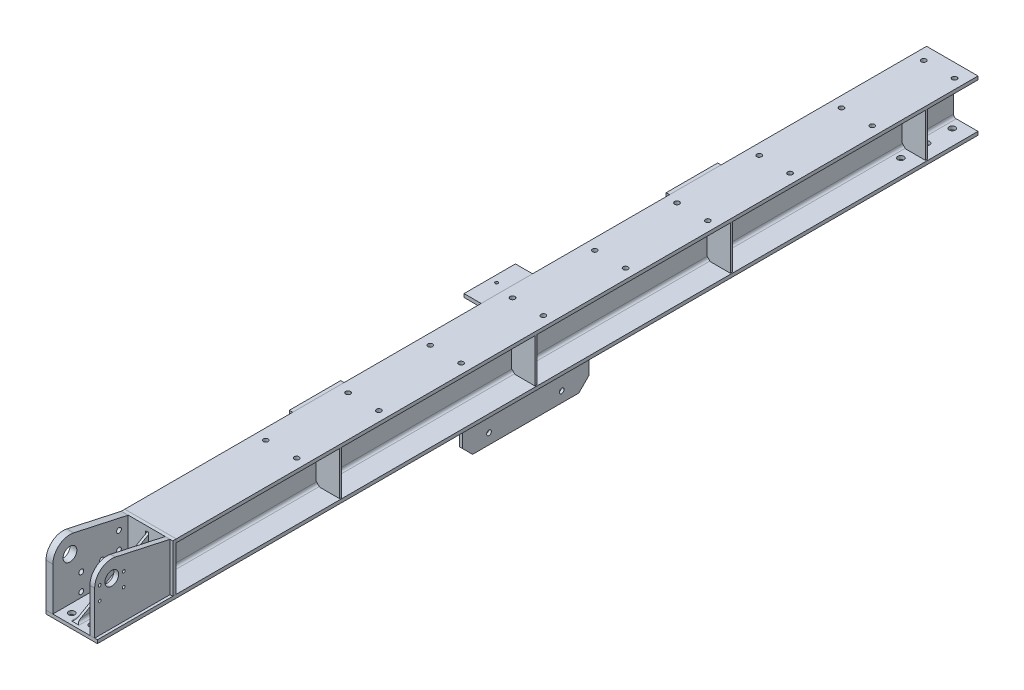
SolidWorks part; units mm, degrees
material "普通碳钢"
ref_plane "前视基准面" through (0, 0, 0) normal (0, 0, 1) x (1, 0, 0)
ref_plane "上视基准面" through (0, 0, 0) normal (0, 1, 0) x (1, 0, 0)
ref_plane "右视基准面" through (0, 0, 0) normal (1, 0, 0) x (0, 0, -1)
sketch "草图1" plane through (0, 0, 0) normal (1, 0, 0) x (0, 0, -1)
  line L0 (-4785.4173, -945.0599) -> (-7355.4173, -945.0599)
  dimension "D1" = 2570
other "H型钢 HW150(1)"
ref_plane "基准面5" through (75, -1020.0599, 4785.4173) normal (0, 0, 1) x (1, 0, 0)
sketch "草图12" plane through (75, -1020.0599, 4785.4173) normal (0, 0, 1) x (1, 0, 0)
  line L0 (-75, -75) -> (75, -75)
  line L1 (75, -75) -> (75, -65)
  line L2 (75, -65) -> (11.5, -65)
  line L3 (3.5, -57) -> (3.5, 57)
  line L4 (11.5, 65) -> (75, 65)
  line L5 (75, 65) -> (75, 75)
  line L6 (75, 75) -> (-75, 75)
  line L7 (0, 75) -> (0, -75) construction
  line L11 (0, 60) -> (0, 75) construction
  line L14 (-75, -75) -> (-75, -65)
  line L15 (-75, -65) -> (-11.5, -65)
  line L16 (-3.5, -57) -> (-3.5, 57)
  line L17 (-11.5, 65) -> (-75, 65)
  line L18 (-75, 65) -> (-75, 75)
  arc A2 (11.5, -65) -> (3.5, -57) centre (11.5, -57) cw
  arc A3 (3.5, 57) -> (11.5, 65) centre (11.5, 57) cw
  arc A5 (-11.5, -65) -> (-3.5, -57) centre (-11.5, -57) ccw
  arc A6 (-3.5, 57) -> (-11.5, 65) centre (-11.5, 57) ccw
  point P2 (0, 0)
  point P38 (0, 0)
  point P39 (75, 75)
  point P40 (75, -75)
  point P41 (-75, -75)
  dimension "D8" = 8
  dimension "D1" = 7
  dimension "D2" = 10
  dimension "D3" = 150
  dimension "D4" = 150
  dimension "D9" = 0
sketch "草图13" plane through (150, 0, 0) normal (1, 0, 0) x (0, 0, -1)
  line L0 (-7355.4173, -945.0599) -> (-7125.4173, -945.0599)
  line L1 (-4785.4173, -945.0599) -> (-7355.4173, -945.0599) construction
  line L2 (-7125.4173, -945.0599) -> (-7125.4173, -960.0599)
  line L6 (-7355.4173, -945.0599) -> (-7355.4173, -1085.0599)
  line L8 (-7355.4173, -1077.0599) -> (-7355.4173, -963.0599) construction
  line L9 (-7355.4173, -1085.0599) -> (-4785.4173, -1085.0599) construction
  line L10 (-7355.4173, -1085.0599) -> (-7345.4173, -1085.0599)
  line L11 (-7355.4173, -1085.0599) -> (-4785.4173, -1085.0599) construction
  line L12 (-7345.4173, -1085.0599) -> (-7125.4173, -960.0599)
  dimension "D1" = 230
  dimension "D2" = 15
  dimension "D3" = 10
extrude "切除-拉伸1" cut sketch "草图13" against normal up to vertex (150 mm away) up to point (0, -945.0599, 7355.4173)
sketch "草图14" plane through (0, 0, 7125.4173) normal (0, 0, 1) x (1, 0, 0)
  line L1 (0, -945.0599) -> (150, -945.0599)
  line L2 (0, -945.0599) -> (0, -1085.0599)
  line L3 (0, -1085.0599) -> (62.0858, -1085.0599)
  line L4 (150, -945.0599) -> (150, -1085.0599)
  line L8 (71, -959.0599) -> (79, -959.0599)
  line L9 (71, -959.0599) -> (71, -1076.1457)
  line L10 (79, -959.0599) -> (79, -1076.1457)
  line L14 (87.9142, -1085.0599) -> (150, -1085.0599)
  line L15 (71.5, -1077.0599) -> (63.5, -1085.0599) construction
  line L16 (71, -1076.1457) -> (62.0858, -1085.0599)
  line L17 (79, -1076.1457) -> (87.9142, -1085.0599)
  line L18 (78.5, -1077.0599) -> (86.5, -1085.0599) construction
  line L19 (79.2721, -1076.4178) -> (87.2071, -1084.3528) construction
  line L20 (70.7284, -1076.4173) -> (62.7929, -1084.3528) construction
  line L23 (78.565, -1077.1249) -> (86.5, -1085.0599) construction
  line L24 (71.4355, -1077.1244) -> (63.5, -1085.0599) construction
  line L25 (78.5, -963.0599) -> (78.5, -1077.0599) construction
  line L26 (71.5, -1077.0599) -> (71.5, -963.0599) construction
  line L27 (70.9162, -960.0599) -> (79.0838, -960.0599) construction
  arc A0 (78.5, -1077.0599) -> (86.5, -1085.0599) centre (86.5, -1077.0599) ccw construction
  point P14 (75, -959.0599)
  dimension "D1" = 0.5
  dimension "D2" = 0.5
  dimension "D3" = 1
  dimension "D4" = 1
  dimension "D5" = 1
extrude "凸台-拉伸1" add sketch "草图14" along normal blind 10 separate body contours L4 L14 L17 L10 L8 L9 L16 L3 L2 L1
sketch "草图15" plane through (0, -1095.0599, 0) normal (0, -1, 0) x (1, 0, 0)
  line L0 (75, 7355.4173) -> (75, 4785.4173) construction
  line L1 (0, 7355.4173) -> (150, 7355.4173) construction
  line L2 (0, 4785.4173) -> (150, 4785.4173) construction
  line L3 (105, 7355.4173) -> (105, 4785.4173) construction
  line L4 (45, 7355.4173) -> (45, 4785.4173) construction
  line L6 (0, 7250.4173) -> (150, 7250.4173) construction
  line L7 (0, 7325.4173) -> (150, 7325.4173)
  line L8 (0, 7325.4173) -> (150, 7325.4173) construction
  line L9 (0, 7175.4173) -> (150, 7175.4173) construction
  line L11 (0, 4890.4173) -> (150, 4890.4173) construction
  line L12 (0, 4815.4173) -> (150, 4815.4173)
  line L13 (0, 4815.4173) -> (150, 4815.4173) construction
  line L14 (0, 4965.4173) -> (150, 4965.4173) construction
  circle A0 centre (105, 7325.4173) radius 9
  circle A1 centre (45, 7325.4173) radius 9
  circle A2 centre (45, 7250.4173) radius 9
  circle A3 centre (105, 7250.4173) radius 9
  circle A4 centre (105, 7175.4173) radius 9
  circle A5 centre (45, 7175.4173) radius 9
  circle A6 centre (105, 4965.4173) radius 9
  circle A7 centre (45, 4965.4173) radius 9
  circle A8 centre (105, 4890.4173) radius 9
  circle A9 centre (45, 4890.4173) radius 9
  circle A10 centre (45, 4815.4173) radius 9
  circle A11 centre (105, 4815.4173) radius 9
  dimension "D9" = 18
  dimension "D1" = 30
  dimension "D2" = 30
  dimension "D3" = 30
  dimension "D4" = 75
  dimension "D5" = 75
  dimension "D6" = 30
  dimension "D7" = 75
  dimension "D8" = 75
extrude "切除-拉伸2" cut sketch "草图15" against normal up to next (10 mm away)
ref_plane "基准面6" through (142, 0, 0) normal (1, 0, 0) x (0, 0, -1)
sketch "草图17" plane through (142, 0, 0) normal (1, 0, 0) x (0, 0, -1)
  line L0 (-7135.4173, -945.0599) -> (-7135.4173, -1085.0599)
  line L1 (-7135.4173, -1085.0599) -> (-7355.4173, -1085.0599)
  line L2 (-7355.4173, -1095.0599) -> (-7355.4173, -1085.0599) construction
  line L3 (-7355.4173, -1085.0599) -> (-4785.4173, -1085.0599) construction
  line L4 (-7355.4173, -1085.0599) -> (-7355.4173, -959.0599)
  line L6 (-7135.4173, -945.0599) -> (-7294.734, -910.2146)
  arc A0 (-7294.734, -910.2146) -> (-7355.4173, -959.0599) centre (-7305.4173, -959.0599) ccw
  dimension "D1" = 100
  dimension "D2" = 126
extrude "凸台-拉伸2" add sketch "草图17" against normal blind 14 separate body
sketch "草图18" plane through (0, 0, 0) normal (-1, 0, 0) x (0, 0, 1)
  line L4 (7294.734, -910.2146) -> (7135.4173, -945.0599)
  line L5 (7135.4173, -945.0599) -> (7135.4173, -1085.0599)
  line L6 (7135.4173, -1085.0599) -> (7355.4173, -1085.0599)
  line L7 (7355.4173, -1085.0599) -> (7355.4173, -959.0599)
  line L8 (7294.734, -910.2146) -> (7135.4173, -945.0599)
  line L9 (7135.4173, -945.0599) -> (7135.4173, -1085.0599)
  line L10 (7135.4173, -1085.0599) -> (7355.4173, -1085.0599)
  line L11 (7355.4173, -1085.0599) -> (7355.4173, -959.0599)
  arc A1 (7355.4173, -959.0599) -> (7294.734, -910.2146) centre (7305.4173, -959.0599) ccw
  arc A2 (7355.4173, -959.0599) -> (7294.734, -910.2146) centre (7305.4173, -959.0599) ccw
  dimension "D1" = 0
extrude "凸台-拉伸3" add sketch "草图18" against normal blind 20 separate body
sketch "草图19" plane through (142, 0, 0) normal (1, 0, 0) x (0, 0, -1)
  line L0 (-7355.4173, -1095.0599) -> (-4785.4173, -1095.0599) construction
  line L1 (-7355.4173, -959.0599) -> (-7355.4173, -1085.0599) construction
  circle A0 centre (-7305.4173, -958.5599) radius 20
  dimension "D1" = 40
  dimension "D2" = 136.5
  dimension "D3" = 50
extrude "切除-拉伸3" cut sketch "草图19" against normal up to surface (142 mm away)
sketch "草图21" plane through (0, 0, 0) normal (-1, 0, 0) x (0, 0, 1)
  line L0 (7272.4173, -1085.0599) -> (7272.4173, -849.2826) construction
  line L1 (7135.4173, -1085.0599) -> (7355.4173, -1085.0599) construction
  line L2 (7212.4173, -1085.0599) -> (7212.4173, -837.7105) construction
  line L3 (7355.4173, -1085.0599) -> (4785.4173, -1085.0599) construction
  line L4 (7162.4173, -1085.0599) -> (7162.4173, -843.584) construction
  line L5 (7355.4173, -1070.0599) -> (7216.7399, -1070.0599) construction
  line L6 (7355.4173, -1085.0599) -> (7355.4173, -959.0599) construction
  line L7 (7355.4173, -1020.0599) -> (7216.7399, -1020.0599) construction
  line L8 (7355.4173, -970.0599) -> (7216.7399, -970.0599) construction
  line L9 (7355.4173, -1095.0599) -> (4785.4173, -1095.0599) construction
  circle A0 centre (7162.4173, -1070.0599) radius 7
  circle A1 centre (7162.4173, -1020.0599) radius 7
  circle A2 centre (7212.4173, -1070.0599) radius 7
  circle A3 centre (7212.4173, -1020.0599) radius 7
  circle A4 centre (7162.4173, -970.0599) radius 7
  circle A5 centre (7272.4173, -1020.0599) radius 7
  circle A6 centre (7272.4173, -1070.0599) radius 7
  dimension "D7" = 14
  dimension "D1" = 25
  dimension "D2" = 50
  dimension "D3" = 50
  dimension "D4" = 83
  dimension "D5" = 60
  dimension "D6" = 50
extrude "切除-拉伸4" cut sketch "草图21" against normal up to next (20 mm away)
sketch "草图22" plane through (142, 0, 0) normal (1, 0, 0) x (0, 0, -1)
  line L0 (-7305.4173, -938.5599) -> (-7305.4173, -1002.3545) construction
  line L1 (-7305.4173, -958.5599) -> (-7241.7897, -958.5599) construction
  line L2 (-7305.4173, -958.5599) -> (-7346.9367, -958.5599) construction
  line L3 (-7270.4173, -958.5599) -> (-7270.4173, -996.2544) construction
  line L4 (-7223.4756, -998.5599) -> (-7340.4173, -998.5599) construction
  line L5 (-7340.4173, -958.5599) -> (-7340.4173, -996.2544) construction
  circle A0 centre (-7305.4173, -958.5599) radius 20 construction
  circle A1 centre (-7340.4173, -958.5599) radius 4
  circle A2 centre (-7270.4173, -958.5599) radius 4
  circle A3 centre (-7340.4173, -998.5599) radius 4
  circle A4 centre (-7270.4173, -998.5599) radius 4
  circle A5 centre (-7305.4173, -958.5599) radius 20 construction
  dimension "D1" = 40
  dimension "D2" = 8
  dimension "D3" = 8
  dimension "D4" = 8
  dimension "D5" = 8
  dimension "D6" = 35
  dimension "D7" = 35
extrude "切除-拉伸5" cut sketch "草图22" against normal up to next (14 mm away)
sketch "草图23" plane through (0, -1095.0599, 0) normal (0, -1, 0) x (1, 0, 0)
  line L0 (150, 7355.4173) -> (150, 4785.4173) construction
  line L1 (71, 6219.4173) -> (79, 6219.4173)
  line L2 (71, 6219.4173) -> (71, 5849.4173)
  line L3 (71, 5849.4173) -> (79, 5849.4173)
  line L4 (79, 6219.4173) -> (79, 5849.4173)
  line L5 (150, 6034.4173) -> (0, 6034.4173) construction
  line L8 (150, 4785.4173) -> (86.5, 4785.4173) construction
  dimension "D1" = 8
  dimension "D2" = 71
  dimension "D3" = 370
  dimension "D4" = 1249
extrude "凸台-拉伸5" add sketch "草图23" along normal blind 140 separate body
chamfer "倒角1" distance 30 angle 45 2 edges at (75, -1235.0599, 5849.4173) (75, -1235.0599, 6219.4173)
sketch "草图24" plane through (79, 0, 0) normal (1, 0, 0) x (0, 0, -1)
  line L0 (-6034.4173, -1235.0599) -> (-6034.4173, -1095.0599) construction
  line L1 (-5879.4173, -1235.0599) -> (-6189.4173, -1235.0599) construction
  line L2 (-5849.4173, -1095.0599) -> (-6219.4173, -1095.0599) construction
  line L3 (-6101.4173, -1235.0599) -> (-6101.4173, -1095.0599) construction
  line L4 (-5969.4173, -1235.0599) -> (-5969.4173, -1095.0599) construction
  line L6 (-6101.4173, -1135.0599) -> (-6172.825, -1258.7418) construction
  line L7 (-5849.4173, -1135.0599) -> (-6219.4173, -1135.0599)
  line L8 (-5849.4173, -1135.0599) -> (-6219.4173, -1135.0599) construction
  line L9 (-5969.4173, -1135.0599) -> (-5957.8759, -1155.0503) construction
  circle A0 centre (-6101.4173, -1135.0599) radius 7
  circle A1 centre (-5969.4173, -1135.0599) radius 7
  circle A2 centre (-6141.4173, -1204.342) radius 7
  circle A3 centre (-5929.4173, -1204.342) radius 7
  dimension "D4" = 14
  dimension "D5" = 14
  dimension "D8" = 14
  dimension "D9" = 14
  dimension "D1" = 67
  dimension "D6" = 30
  dimension "D7" = 30
  dimension "D10" = 80
  dimension "D11" = 80
  dimension "D2" = 65
  dimension "D3" = 40
extrude "切除-拉伸6" cut sketch "草图24" against normal up to next (8 mm away)
sketch "草图26" plane through (0, 0, 4785.4173) normal (0, 0, -1) x (-1, 0, 0)
  line L0 (0, -955.0599) -> (-63.5, -955.0599) construction
  line L1 (0, -955.0599) -> (-10, -955.0599)
  line L2 (0, -955.0599) -> (0, -1085.0599)
  line L3 (0, -1085.0599) -> (-10, -1085.0599)
  line L4 (-10, -955.0599) -> (-10, -1085.0599)
  line L5 (-63.5, -1085.0599) -> (0, -1085.0599) construction
  line L6 (0, -945.0599) -> (0, -955.0599) construction
  dimension "D1" = 10
extrude "凸台-拉伸7" add sketch "草图26" against normal blind 148 separate body
sketch "草图27" plane through (0, 0, 0) normal (-1, 0, 0) x (0, 0, 1)
  line L0 (4810.4173, -970.0599) -> (4908.4173, -970.0599) construction
  line L1 (4908.4173, -970.0599) -> (4908.4173, -1070.0599) construction
  line L2 (4908.4173, -1070.0599) -> (4810.4173, -1070.0599) construction
  line L3 (4810.4173, -1070.0599) -> (4810.4173, -970.0599) construction
  line L4 (4810.4173, -1020.0599) -> (4908.4173, -1020.0599) construction
  line L7 (7125.4173, -945.0599) -> (4785.4173, -945.0599) construction
  circle A0 centre (4810.4173, -970.0599) radius 7
  circle A1 centre (4908.4173, -970.0599) radius 7
  circle A2 centre (4810.4173, -1070.0599) radius 7
  circle A3 centre (4908.4173, -1070.0599) radius 7
  circle A4 centre (4908.4173, -1020.0599) radius 7
  circle A5 centre (4810.4173, -1020.0599) radius 6.9618
  dimension "D1" = 98
  dimension "D2" = 50
  dimension "D3" = 50
  dimension "D4" = 25
extrude "切除-拉伸7" cut sketch "草图27" against normal up to next (10 mm away)
sketch "草图28" plane through (0, -945.0599, 0) normal (0, 1, 0) x (1, 0, 0)
  line L0 (121.5, -4825.4173) -> (121.5, -6745.4173) construction
  line L2 (31.5, -6745.4173) -> (31.5, -4825.4173) construction
  line L3 (31.5, -4825.4173) -> (121.5, -4825.4173) construction
  line L4 (31.5, -5065.4173) -> (121.5, -5065.4173) construction
  line L5 (31.5, -5305.4173) -> (121.5, -5305.4173) construction
  line L6 (31.5, -5545.4173) -> (121.5, -5545.4173) construction
  line L7 (31.5, -5785.4173) -> (121.5, -5785.4173) construction
  line L8 (31.5, -6025.4173) -> (121.5, -6025.4173) construction
  line L9 (31.5, -6265.4173) -> (121.5, -6265.4173) construction
  line L10 (31.5, -6505.4173) -> (121.5, -6505.4173) construction
  line L11 (31.5, -6745.4173) -> (121.5, -6745.4173) construction
  line L13 (150, -7125.4173) -> (150, -4785.4173) construction
  line L14 (86.5, -4785.4173) -> (150, -4785.4173) construction
  circle A0 centre (121.5, -6745.4173) radius 7
  circle A1 centre (31.5, -6745.4173) radius 7
  circle A2 centre (121.5, -6505.4173) radius 7
  circle A3 centre (31.5, -6505.4173) radius 7
  circle A4 centre (121.5, -6265.4173) radius 7
  circle A5 centre (31.5, -6265.4173) radius 7
  circle A6 centre (121.5, -6025.4173) radius 7
  circle A7 centre (31.5, -6025.4173) radius 7
  circle A8 centre (121.5, -5785.4173) radius 7
  circle A9 centre (31.5, -5785.4173) radius 7
  circle A10 centre (121.5, -5545.4173) radius 7
  circle A11 centre (31.5, -5545.4173) radius 7
  circle A12 centre (121.5, -5305.4173) radius 7
  circle A13 centre (31.5, -5305.4173) radius 7
  circle A14 centre (121.5, -5065.4173) radius 7
  circle A15 centre (31.5, -5065.4173) radius 7
  circle A16 centre (121.5, -4825.4173) radius 7
  circle A17 centre (31.5, -4825.4173) radius 7
  dimension "D1" = 9
  dimension "D6" = 14
  dimension "D2" = 240
  dimension "D3" = 90
  dimension "D4" = 28.5
  dimension "D5" = 40
extrude "切除-拉伸8" cut sketch "草图28" against normal up to next (10 mm away)
ref_plane "基准面7" through (0, 0, 4935.4173) normal (0, 0, -1) x (-1, 0, 0)
sketch "草图29" plane through (0, 0, 4935.4173) normal (0, 0, -1) x (-1, 0, 0)
  line L1 (-147, -955.0599) -> (-88.5, -955.0599)
  line L2 (-147, -955.0599) -> (-147, -1085.0599)
  line L3 (-147, -1085.0599) -> (-88.5, -1085.0599)
  line L4 (-78.5, -965.0599) -> (-78.5, -1075.0599)
  line L5 (-86.5, -955.0599) -> (-150, -955.0599) construction
  line L6 (-78.5, -1077.0599) -> (-78.5, -963.0599) construction
  line L7 (-150, -1085.0599) -> (-86.5, -1085.0599) construction
  line L8 (-150, -1095.0599) -> (-150, -1085.0599) construction
  line L9 (-88.5, -955.0599) -> (-78.5, -965.0599)
  line L10 (-88.5, -1085.0599) -> (-78.5, -1075.0599)
  point P1 (-78.5, -1085.0599)
  point P3 (-78.5, -955.0599)
  dimension "D1" = 3
extrude "凸台-拉伸8" add sketch "草图29" along normal blind 6 separate body
pattern_linear "阵列(线性)1" count 4 spacing 570 along (0, 0, 1) of "凸台-拉伸8"
sketch "草图30" plane through (0, 0, 0) normal (-1, 0, 0) x (0, 0, 1)
  line L0 (7125.4173, -945.0599) -> (4785.4173, -945.0599) construction
  line L1 (5385.4173, -945.0599) -> (5535.4173, -945.0599)
  line L2 (5385.4173, -945.0599) -> (5385.4173, -1095.0599)
  line L3 (5385.4173, -1095.0599) -> (5535.4173, -1095.0599)
  line L4 (5535.4173, -945.0599) -> (5535.4173, -1095.0599)
  line L5 (7355.4173, -1095.0599) -> (4785.4173, -1095.0599) construction
  line L6 (4785.4173, -1085.0599) -> (4785.4173, -955.0599) construction
  line L15 (5460.4173, -945.0599) -> (5460.4173, -1095.0599) construction
  line L16 (5385.4173, -970.0599) -> (5535.4173, -970.0599) construction
  line L17 (5535.4173, -970.0599) -> (5535.4173, -1070.0599) construction
  line L18 (5535.4173, -1070.0599) -> (5385.4173, -1070.0599) construction
  line L19 (7125.4173, -955.0599) -> (4785.4173, -955.0599) construction
  line L20 (7355.4173, -1085.0599) -> (4785.4173, -1085.0599) construction
  line L21 (5425.4173, -945.0599) -> (5425.4173, -1095.0599) construction
  line L22 (5495.4173, -945.0599) -> (5495.4173, -1095.0599) construction
  line L23 (5420.4173, -970.0599) -> (5420.4173, -1070.0599)
  line L24 (5430.4173, -970.0599) -> (5430.4173, -1070.0599)
  line L25 (5490.4173, -970.0599) -> (5490.4173, -1070.0599)
  line L26 (5500.4173, -970.0599) -> (5500.4173, -1070.0599)
  arc A0 (5430.4173, -970.0599) -> (5420.4173, -970.0599) centre (5425.4173, -970.0599) ccw
  arc A1 (5420.4173, -1070.0599) -> (5430.4173, -1070.0599) centre (5425.4173, -1070.0599) ccw
  arc A2 (5490.4173, -1070.0599) -> (5500.4173, -1070.0599) centre (5495.4173, -1070.0599) ccw
  arc A3 (5500.4173, -970.0599) -> (5490.4173, -970.0599) centre (5495.4173, -970.0599) ccw
  dimension "D2" = 5
  dimension "D1" = 150
  dimension "D6" = 600
  dimension "D7" = 15
  dimension "D8" = 15
  dimension "D9" = 35
  dimension "D10" = 35
extrude "凸台-拉伸9" add sketch "草图30" along normal blind 10 separate body
pattern_linear "阵列(线性)2" count 3 spacing 550 along (0, 0, 1) of "凸台-拉伸9"
sketch "草图32" plane through (-10, 0, 0) normal (-1, 0, 0) x (0, 0, 1)
  line L0 (5535.4173, -1095.0599) -> (5535.4173, -945.0599) construction
  line L1 (5385.4173, -1095.0599) -> (5535.4173, -1095.0599)
  line L2 (5385.4173, -1095.0599) -> (5385.4173, -1085.0599)
  line L3 (5385.4173, -1085.0599) -> (5535.4173, -1085.0599)
  line L4 (5535.4173, -1095.0599) -> (5535.4173, -1085.0599)
  dimension "D1" = 10
extrude "凸台-拉伸10" add sketch "草图32" along normal blind 40
fillet "圆角1" radius 4 1 edges at (-10, -1085.0599, 5460.4173)
sketch "草图33" plane through (-10, 0, 0) normal (-1, 0, 0) x (0, 0, 1)
  line L1 (5935.4173, -945.0599) -> (6085.4173, -945.0599)
  line L2 (5935.4173, -945.0599) -> (5935.4173, -955.0599)
  line L3 (5935.4173, -955.0599) -> (6085.4173, -955.0599)
  line L4 (6085.4173, -945.0599) -> (6085.4173, -955.0599)
  dimension "D1" = 10
extrude "凸台-拉伸11" add sketch "草图33" along normal blind 40
fillet "圆角2" radius 4 1 edges at (-10, -955.0599, 6010.4173)
sketch "草图34" plane through (-10, 0, 0) normal (-1, 0, 0) x (0, 0, 1)
  line L0 (6635.4173, -1095.0599) -> (6635.4173, -945.0599) construction
  line L1 (6485.4173, -1095.0599) -> (6635.4173, -1095.0599)
  line L2 (6485.4173, -1095.0599) -> (6485.4173, -1085.0599)
  line L3 (6485.4173, -1085.0599) -> (6635.4173, -1085.0599)
  line L4 (6635.4173, -1095.0599) -> (6635.4173, -1085.0599)
  dimension "D1" = 10
extrude "凸台-拉伸12" add sketch "草图34" along normal blind 40
fillet "圆角3" radius 4 1 edges at (-10, -1085.0599, 6560.4173)
hole_wizard "M10 螺纹孔1" positions "草图35" profile "草图36" tap size "M10" standard "GB" end condition up to next
sketch "草图35" plane through (0, -945.0599, 0) normal (0, 1, 0) x (1, 0, 0)
  line L0 (-50, -5935.4173) -> (0, -5935.4173) construction
  line L1 (-50, -6085.4173) -> (-50, -5935.4173) construction
  point P0 (-30, -6010.4173)
  dimension "D1" = 75
  dimension "D2" = 20
sketch "草图36" plane through (-30, -945.0599, 6010.4173) normal (1, 0, 0) x (0, 0, 1)
  line L0 (0, 0) -> (0, 10.001)
  line L1 (0, 10.001) -> (4.25, 10.001)
  line L2 (4.25, 10.001) -> (4.25, 0)
  line L5 (4.25, 0) -> (0, 0)
  line L11 (0, -6.35) -> (0, 107.95) construction
  dimension "通孔螺纹孔钻头直径" = 8.5
  dimension "通孔螺纹孔钻头深度" = 10.001
cosmetic thread "孔螺蚊线1" parameters "D2"=10
hole_wizard "M10 螺纹孔2" positions "3D草图1" profile "草图37" tap size "M10" standard "GB" end condition up to next
sketch3d "3D草图1"
  line L0 (-50, -1095.0599, 5385.4173) -> (-50, -1095.0599, 5535.4173) construction
  line L1 (-50, -1095.0599, 5385.4173) -> (0, -1095.0599, 5385.4173) construction
  line L2 (-50, -1095.0599, 6485.4173) -> (0, -1095.0599, 6485.4173) construction
  line L3 (-50, -1095.0599, 6485.4173) -> (-50, -1095.0599, 6635.4173) construction
  point P0 (-30, -1095.0599, 5460.4173)
  point P2 (-30, -1095.0599, 6560.4173)
  dimension "D1" = 20
  dimension "D2" = 75
  dimension "D3" = 75
  dimension "D4" = 20
sketch "草图37" plane through (-30, -1095.0599, 5460.4173) normal (1, 0, 0) x (0, 0, -1)
  line L0 (0, 0) -> (0, 10.001)
  line L1 (0, 10.001) -> (4.25, 10.001)
  line L2 (4.25, 10.001) -> (4.25, 0)
  line L5 (4.25, 0) -> (0, 0)
  line L11 (0, -6.35) -> (0, 107.95) construction
  dimension "通孔螺纹孔钻头直径" = 8.5
  dimension "通孔螺纹孔钻头深度" = 10.001
cosmetic thread "孔螺蚊线2" parameters "D2"=10
cosmetic thread "孔螺蚊线3" parameters "D2"=10
